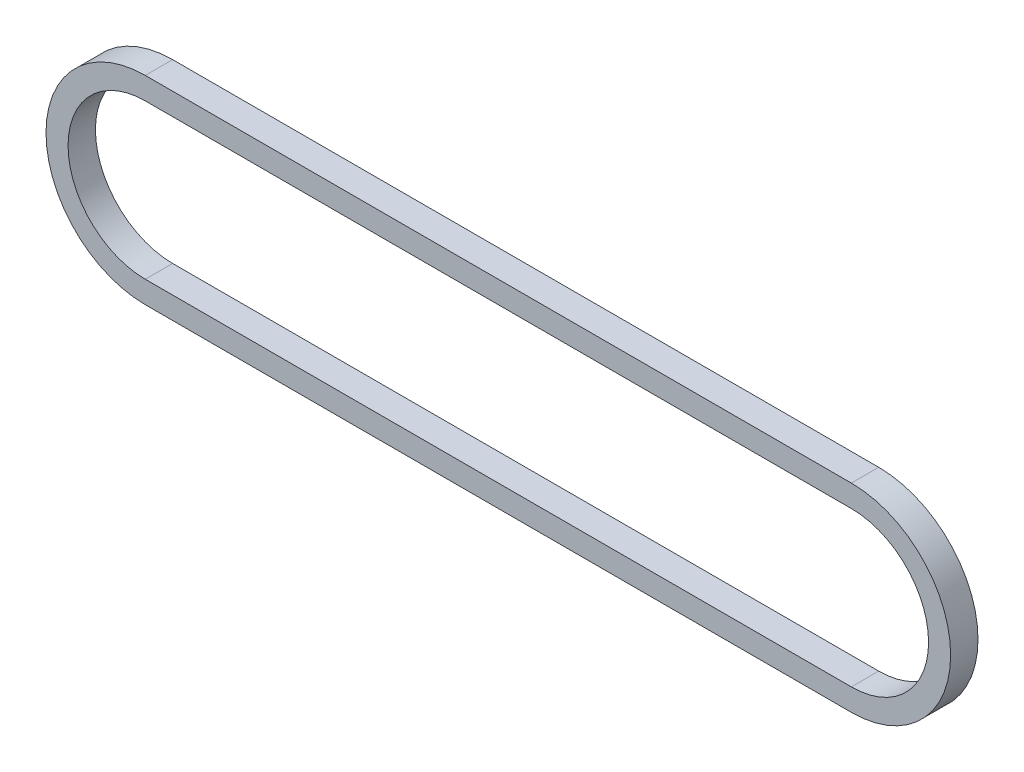
SolidWorks part; units mm, degrees
ref_plane "Front Plane" through (0, 0, 0) normal (0, 0, 1) x (1, 0, 0)
ref_plane "Top Plane" through (0, 0, 0) normal (0, 1, 0) x (1, 0, 0)
ref_plane "Right Plane" through (0, 0, 0) normal (1, 0, 0) x (0, 0, -1)
sketch "Sketch1" plane through (0, 0, 0) normal (0, 0, 1) x (1, 0, 0)
  line L0 (0, 0) -> (203.2, 0) construction
  line L1 (0, 22.225) -> (203.2, 22.225)
  line L2 (0, -22.225) -> (203.2, -22.225)
  line L3 (0, 28.575) -> (203.2, 28.575)
  line L4 (0, -28.575) -> (203.2, -28.575)
  arc A0 (0, 22.225) -> (0, -22.225) centre (0, 0) ccw
  arc A1 (203.2, -22.225) -> (203.2, 22.225) centre (203.2, 0) ccw
  arc A2 (203.2, -28.575) -> (203.2, 28.575) centre (203.2, 0) ccw
  arc A3 (0, 28.575) -> (0, -28.575) centre (0, 0) ccw
  point P3 (101.6, 0)
  dimension "D2" = 22.225
  dimension "D1" = 203.2
  dimension "D3" = 6.35
extrude "Boss-Extrude1" add sketch "Sketch1" along normal blind 7.874
